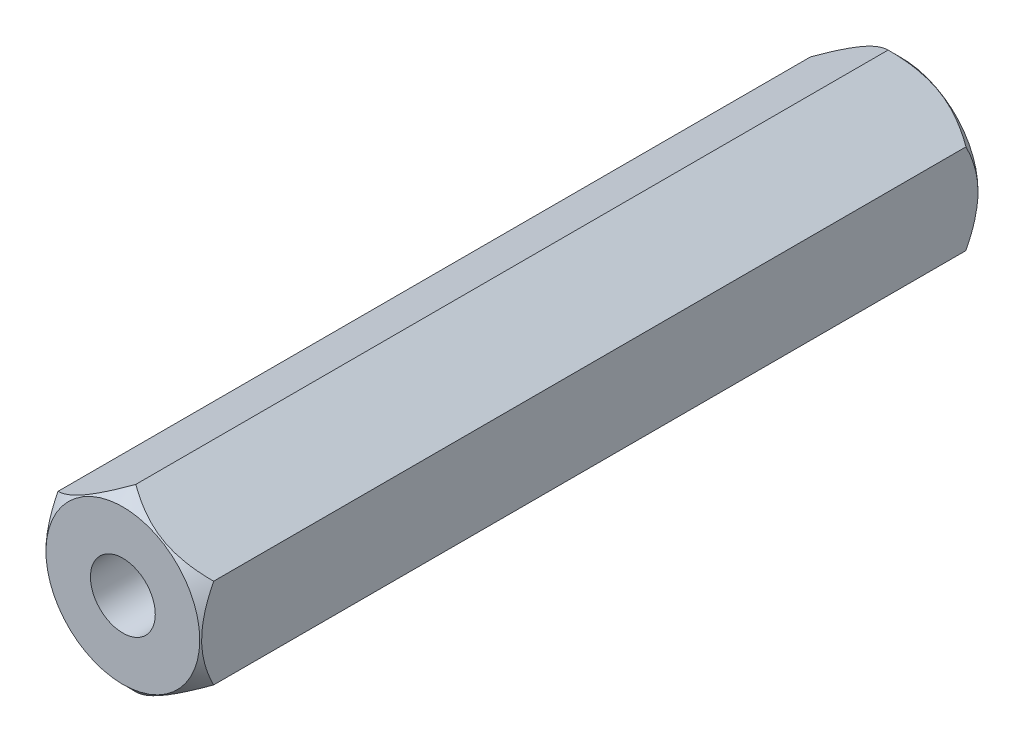
SolidWorks part; units mm, degrees
material "Acero galvanizado"
ref_plane "Alzado" through (0, 0, 0) normal (0, 0, 1) x (1, 0, 0)
ref_plane "Planta" through (0, 0, 0) normal (0, 1, 0) x (1, 0, 0)
ref_plane "Vista lateral" through (0, 0, 0) normal (1, 0, 0) x (0, 0, -1)
sketch "Croquis1" plane through (0, 0, 0) normal (0, 0, 1) x (1, 0, 0)
  line L1 (0, 3.4641) -> (-3, 1.7321)
  line L2 (-3, 1.7321) -> (-3, -1.7321)
  line L3 (-3, -1.7321) -> (0, -3.4641)
  line L4 (0, -3.4641) -> (3, -1.7321)
  line L5 (3, -1.7321) -> (3, 1.7321)
  line L6 (3, 1.7321) -> (0, 3.4641)
  circle A0 centre (0, 0) radius 3 construction
  dimension "D1" = 6
extrude "Saliente-Extruir1" add sketch "Croquis1" along normal mid plane 30
sketch "Croquis2" plane through (0, 0, 0) normal (1, 0, 0) x (0, 0, -1)
  line L0 (15, 1.7321) -> (15, 3.4641) construction
  line L1 (15, 2.9641) -> (19.5, 2.9641)
  line L2 (14.5, 3.4641) -> (14.5, 7.9641)
  line L3 (14.5, 7.9641) -> (19.5, 7.9641)
  line L4 (19.5, 2.9641) -> (19.5, 7.9641)
  line L5 (-15, 3.4641) -> (15, 3.4641) construction
  line L6 (-17.8031, 0) -> (18.6488, 0) construction
  line L7 (-19.5, 2.9641) -> (-19.5, 7.9641)
  line L8 (-14.5, 7.9641) -> (-19.5, 7.9641)
  line L9 (-14.5, 3.4641) -> (-14.5, 7.9641)
  line L10 (-15, 2.9641) -> (-19.5, 2.9641)
  line L11 (15, 2.9641) -> (14.5, 3.4641)
  line L12 (-14.5, 3.4641) -> (-15, 2.9641)
  dimension "D1" = 0.5
  dimension "D5" = 5
  dimension "D6" = 5
  dimension "D7" = 0.5
revolve "Cortar-Revolución2" cut sketch "Croquis2" angle 360 about L6
sketch "Croquis3" plane through (0, 0, 15) normal (0, 0, 1) x (1, 0, 0)
  circle A0 centre (0, 0) radius 1.25
  dimension "D1" = 2.5
extrude "Cortar-Extruir1" cut sketch "Croquis3" against normal blind 30
